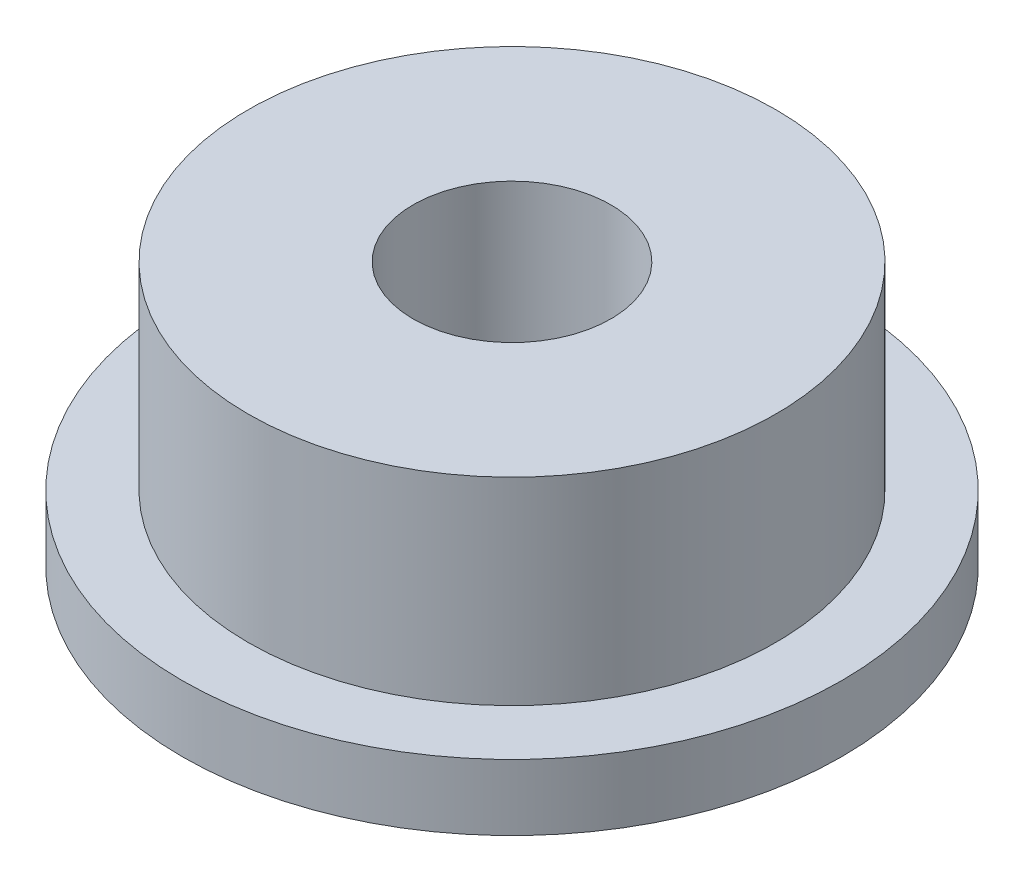
SolidWorks part; units mm, degrees
material "普通碳钢"
ref_plane "前视" through (0, 0, 0) normal (0, 0, 1) x (1, 0, 0)
ref_plane "上视" through (0, 0, 0) normal (0, 1, 0) x (1, 0, 0)
ref_plane "右视" through (0, 0, 0) normal (1, 0, 0) x (0, 0, -1)
sketch "草图1" plane through (0, 0, 0) normal (0, 0, 1) x (1, 0, 0)
  line L0 (0, 0) -> (0, -21.3956) construction
  line L1 (1.5, -4) -> (1.5, 0)
  line L2 (1.5, 0) -> (4, 0)
  line L3 (4, 0) -> (4, -3)
  line L4 (4, -3) -> (5, -3)
  line L5 (5, -3) -> (5, -4)
  line L6 (5, -4) -> (1.5, -4)
  dimension "D1" = 4
  dimension "D2" = 1
  dimension "D3" = 8
  dimension "D4" = 3
  dimension "D5" = 10
revolve "旋转1" add sketch "草图1" angle 360 about L0
